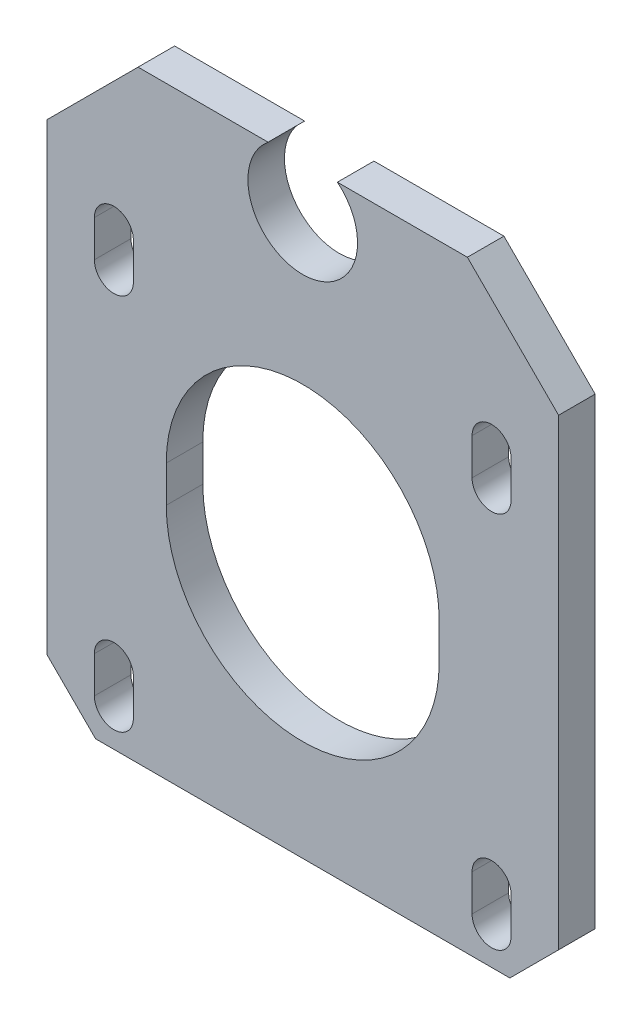
SolidWorks part; units mm, degrees
ref_plane "Front Plane" through (0, 0, 0) normal (0, 0, 1) x (1, 0, 0)
ref_plane "Top Plane" through (0, 0, 0) normal (0, 1, 0) x (1, 0, 0)
ref_plane "Right Plane" through (0, 0, 0) normal (1, 0, 0) x (0, 0, -1)
sketch "Sketch1" plane through (0, 0, 0) normal (0, 0, 1) x (1, 0, 0)
  line L0 (0, 1.5) -> (0, -1.5) construction
  line L1 (-21, -21) -> (21, -21)
  line L2 (-21, -21) -> (-21, 21)
  line L3 (2.8452, 28.4864) -> (13.5136, 28.4864)
  line L4 (0, 12.7) -> (0, -21) construction
  line L5 (-21, -21) -> (21, 21) construction
  line L6 (-21, 21) -> (21, -21) construction
  line L7 (-15.5, 15.5) -> (15.5, 15.5) construction
  line L8 (-15.5, 15.5) -> (-15.5, -15.5) construction
  line L9 (-15.5, -15.5) -> (15.5, -15.5) construction
  line L10 (15.5, 15.5) -> (15.5, -15.5) construction
  line L11 (21, 21) -> (13.5136, 28.4864)
  line L12 (-11.2, 1.5) -> (-11.2, -1.5)
  line L13 (21, -21) -> (21, 21)
  line L14 (11.2, 1.5) -> (11.2, -1.5)
  line L16 (-15.5, -15) -> (-15.5, -18) construction
  line L17 (-13.9, -15) -> (-13.9, -18)
  line L18 (-17.1, -15) -> (-17.1, -18)
  line L19 (-15.5, 16) -> (-15.5, 13) construction
  line L20 (-13.9, 16) -> (-13.9, 13)
  line L21 (-17.1, 16) -> (-17.1, 13)
  line L22 (-21, 21) -> (-13.5136, 28.4864)
  line L23 (15.5, -15) -> (15.5, -18) construction
  line L24 (13.9, -15) -> (13.9, -18)
  line L25 (17.1, -15) -> (17.1, -18)
  line L26 (15.5, 16) -> (15.5, 13) construction
  line L27 (13.9, 16) -> (13.9, 13)
  line L28 (17.1, 16) -> (17.1, 13)
  line L29 (15.5, 15.5) -> (15.5, -15.5) construction
  line L31 (-2.8452, 28.4864) -> (-13.5136, 28.4864)
  circle A0 centre (0, 0) radius 11.2 construction
  circle A1 centre (-15.5, 15.5) radius 1.6 construction
  circle A2 centre (15.5, 15.5) radius 1.6 construction
  circle A3 centre (15.5, -15.5) radius 1.6 construction
  circle A4 centre (-15.5, -15.5) radius 1.6 construction
  arc A5 (13.9, -15) -> (17.1, -15) centre (15.5, -15) cw
  arc A6 (-11.2, -1.5) -> (11.2, -1.5) centre (0, -1.5) ccw
  arc A7 (17.1, -18) -> (13.9, -18) centre (15.5, -18) cw
  arc A8 (13.9, 16) -> (17.1, 16) centre (15.5, 16) cw
  arc A9 (-13.9, -15) -> (-17.1, -15) centre (-15.5, -15) ccw
  arc A10 (-17.1, -18) -> (-13.9, -18) centre (-15.5, -18) ccw
  arc A11 (-13.9, 16) -> (-17.1, 16) centre (-15.5, 16) ccw
  arc A12 (-17.1, 13) -> (-13.9, 13) centre (-15.5, 13) ccw
  arc A13 (-2.8452, 28.4864) -> (2.8452, 28.4864) centre (0, 25) ccw
  arc A14 (17.1, 13) -> (13.9, 13) centre (15.5, 13) cw
  arc A15 (11.2, 1.5) -> (-11.2, 1.5) centre (0, 1.5) ccw
  circle A16 centre (15.5, -15.5) radius 1.6 construction
  circle A17 centre (15.5, 15.5) radius 1.6 construction
  point P17 (0, 0)
  point P26 (15.5, -16.5)
  point P29 (-15.5, -16.5)
  point P36 (-15.5, 14.5)
  point P52 (15.5, 14.5)
  dimension "D2" = 22.4
  dimension "D4" = 3.2
  dimension "D7" = 9
  dimension "D9" = 11.2
  dimension "D12" = 1.6
  dimension "D13" = 13.5136
  dimension "D15" = 1.5
  dimension "D1" = 42
  dimension "D3" = 31
  dimension "D5" = 21
  dimension "D6" = 25
  dimension "D8" = 2.8452
  dimension "D10" = 1
  dimension "D11" = 1
extrude "Boss-Extrude1" add sketch "Sketch1" along normal blind 3
chamfer "Chamfer1" distance 4 angle 45 2 edges at (-21, -21, 1.5) (21, -21, 1.5)
sketch "Sketch2" [suppressed] plane through (0, 0, 3) normal (0, 0, 1) x (1, 0, 0)
  circle A0 centre (10.55, 9) radius 1.4
  dimension "D1" = 2.8
  dimension "D2" = 9
  dimension "D3" = 10.55
extrude "Cut-Extrude1" [suppressed] cut sketch "Sketch2" against normal through all
